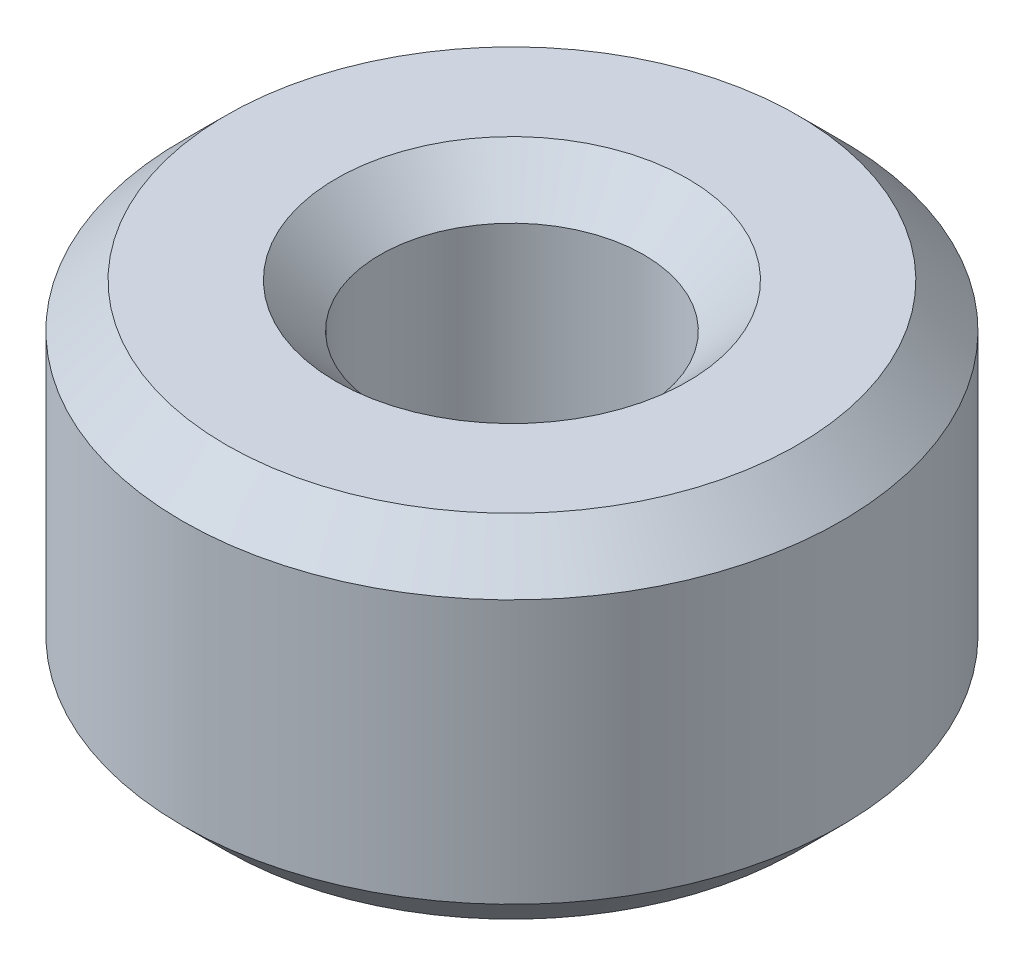
SolidWorks part; units mm, degrees
ref_plane "Front Plane" through (0, 0, 0) normal (0, 0, 1) x (1, 0, 0)
ref_plane "Top Plane" through (0, 0, 0) normal (0, 1, 0) x (1, 0, 0)
ref_plane "Right Plane" through (0, 0, 0) normal (1, 0, 0) x (0, 0, -1)
sketch "Sketch1" plane through (0, 0, 0) normal (0, 1, 0) x (1, 0, 0)
  circle A0 centre (0, 0) radius 3
  circle A1 centre (0, 0) radius 7.5
  dimension "D1" = 6
  dimension "D2" = 15
extrude "Boss-Extrude1" add sketch "Sketch1" along normal blind 8
chamfer "Chamfer1" distance 1 angle 45 4 edges at (0, 0, 3) (0, 0, 7.5) (0, 8, 3) (0, 8, 7.5)
